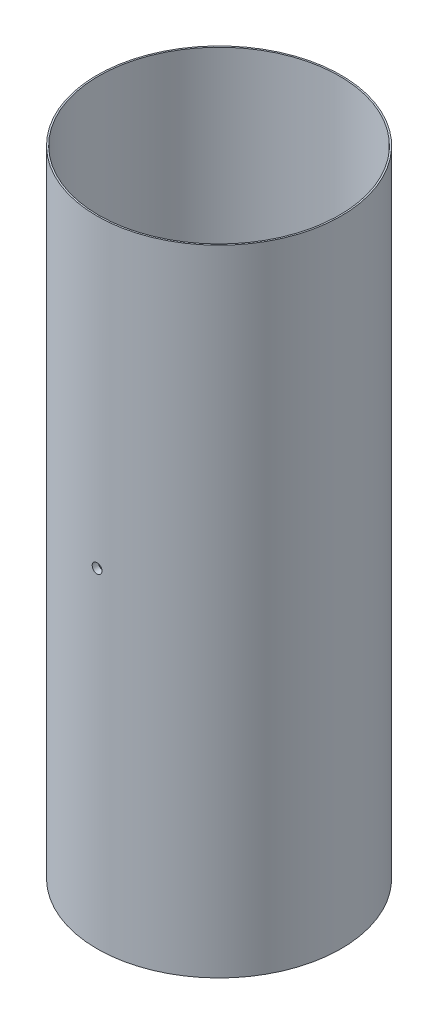
SolidWorks part; units mm, degrees
material "6061-T4 (SS)"
ref_plane "Front Plane" through (0, 0, 0) normal (0, 0, 1) x (1, 0, 0)
ref_plane "Top Plane" through (0, 0, 0) normal (0, 1, 0) x (1, 0, 0)
ref_plane "Right Plane" through (0, 0, 0) normal (1, 0, 0) x (0, 0, -1)
sketch "Sketch1" plane through (0, 0, 0) normal (0, 1, 0) x (1, 0, 0)
  circle A0 centre (0, 0) radius 63.5
  circle A1 centre (0, 0) radius 60.325
  dimension "D1" = 127
  dimension "D2" = 120.65
extrude "Boss-Extrude1" add sketch "Sketch1" along normal blind 330.2
sketch "Sketch5" plane through (0, 0, 0) normal (0, 1, 0) x (1, 0, 0)
  circle A0 centre (0, 0) radius 60.325
  circle A1 centre (0, 0) radius 62.7063
  dimension "D1" = 120.65
  dimension "D2" = 125.4125
extrude "Cut-Extrude1" cut sketch "Sketch5" along normal blind 158.75
sketch "Sketch6" plane through (0, 330.2, 0) normal (0, 1, 0) x (1, 0, 0)
  circle A0 centre (0, 0) radius 60.325
  circle A1 centre (0, 0) radius 62.7063
  dimension "D1" = 120.65
  dimension "D2" = 125.4125
extrude "Cut-Extrude2" cut sketch "Sketch6" against normal blind 120.65
ref_plane "Plane1" through (0, 0, 63.5) normal (0, 0, 1) x (1, 0, 0)
ref_plane "Plane2" through (0, 0, -63.5) normal (0, 0, 1) x (1, 0, 0)
sketch "Sketch8" plane through (0, 0, 63.5) normal (0, 0, 1) x (1, 0, 0)
  circle A0 centre (0, 171.45) radius 6.4556
  dimension "D1" = 171.45
sketch "Sketch12" plane through (0, 0, -63.5) normal (0, 0, 1) x (1, 0, 0)
  circle A0 centre (0, 171.45) radius 6.4556
hole_wizard "Tap Drill for 1/4-20 Tap8" positions "Sketch20" profile "Sketch19" hole size "1/4-20" standard "ANSI Inch"
sketch "Sketch20" plane through (0, 0, 63.5) normal (0, 0, 1) x (1, 0, 0)
  point P0 (0, 171.45)
sketch "Sketch19" plane through (0, 171.45, 63.5) normal (1, 0, 0) x (0, -1, 0)
  line L0 (0, 0) -> (0, 3.175)
  line L1 (0, 3.175) -> (2.5527, 3.175)
  line L2 (2.5527, 3.175) -> (2.5527, 0)
  line L5 (2.5527, 0) -> (0, 0)
  line L11 (0, -6.35) -> (0, 107.95) construction
  dimension "Thru Hole Dia." = 5.1054
  dimension "Thru Hole Depth" = 3.175
hole_wizard "Tap Drill for 1/4-20 Tap9" positions "Sketch21" profile "Sketch22" hole size "1/4-20" standard "ANSI Inch"
sketch "Sketch21" plane through (0, 0, -63.5) normal (0, 0, 1) x (1, 0, 0)
  point P0 (0, 171.45)
sketch "Sketch22" plane through (0, 171.45, -63.5) normal (1, 0, 0) x (0, 1, 0)
  line L0 (0, 0) -> (0, 3.175)
  line L1 (0, 3.175) -> (2.5527, 3.175)
  line L2 (2.5527, 3.175) -> (2.5527, 0)
  line L5 (2.5527, 0) -> (0, 0)
  line L11 (0, -6.35) -> (0, 107.95) construction
  dimension "Thru Hole Dia." = 5.1054
  dimension "Thru Hole Depth" = 3.175
ref_plane "Plane3" through (0, 313.5439, 0) normal (0, 1, 0) x (1, 0, 0)
sketch "Sketch24" plane through (0, 313.5439, 0) normal (0, 1, 0) x (1, 0, 0)
  circle A0 centre (0, 0) radius 60.325
sketch "Sketch25" plane through (0, 0, 0) normal (0, 0, 1) x (1, 0, 0)
  point P0 (0, 171.45)
sketch "Sketch28" plane through (0, 0, 0) normal (1, 0, 0) x (0, 0, -1)
  line L0 (0, 171.45) -> (-150.2291, 171.45) construction
  line L1 (-150.2291, 171.45) -> (0, 171.45) construction
  line L2 (0, 171.45) -> (137.0328, 171.45) construction
sketch "Sketch29" plane through (0, 0, 0) normal (0, 0, 1) x (1, 0, 0)
  line L0 (110.9363, 171.45) -> (-138.7821, 171.45) construction
